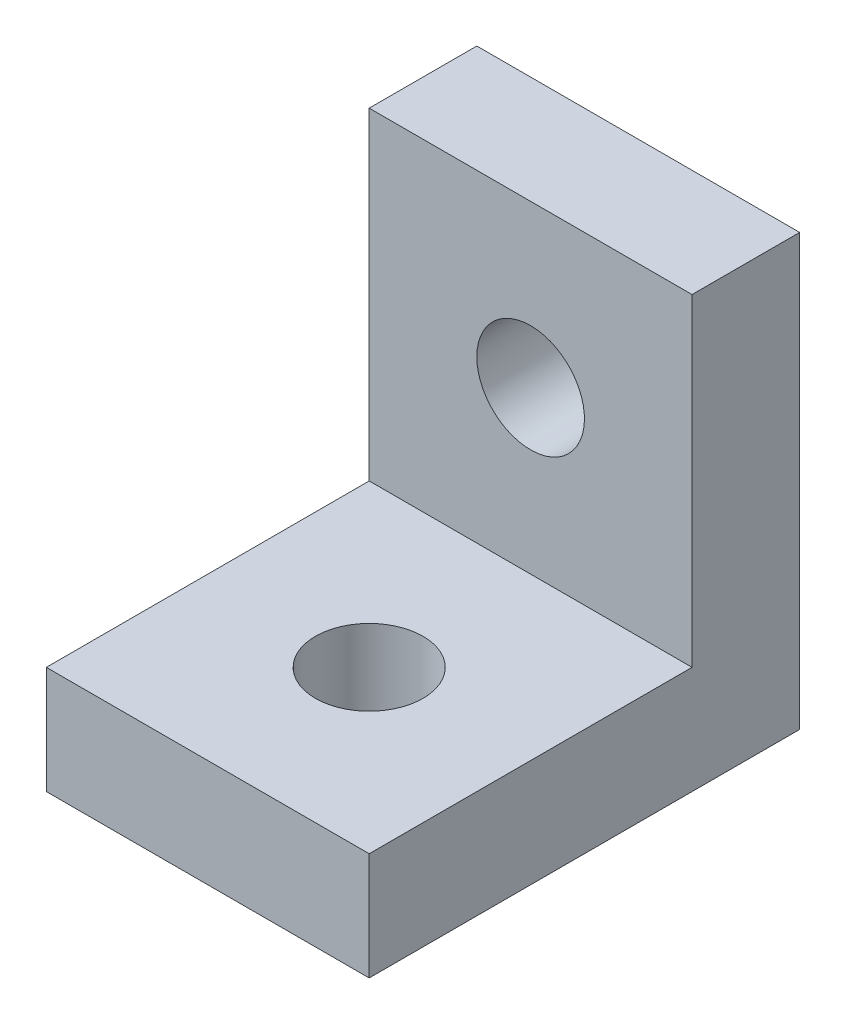
SolidWorks part; units mm, degrees
ref_plane "Front Plane" through (0, 0, 0) normal (0, 0, 1) x (1, 0, 0)
ref_plane "Top Plane" through (0, 0, 0) normal (0, 1, 0) x (1, 0, 0)
ref_plane "Right Plane" through (0, 0, 0) normal (1, 0, 0) x (0, 0, -1)
sketch "Sketch1" plane through (0, 0, 0) normal (1, 0, 0) x (0, 0, -1)
  line L0 (0, 40) -> (0, 0)
  line L1 (0, 0) -> (-40, 0)
  line L2 (-10, 40) -> (-10, 10)
  line L3 (-10, 10) -> (-40, 10)
  line L4 (0, 40) -> (-10, 40)
  line L5 (-40, 0) -> (-40, 10)
  dimension "D1" = 40
  dimension "D2" = 10
extrude "Boss-Extrude1" add sketch "Sketch1" along normal mid plane 30
sketch "Sketch2" plane through (0, 0, 0) normal (0, 0, -1) x (-1, 0, 0)
  line L0 (0, 22) -> (0, -22) construction
  line L1 (-15, 0) -> (15, 0) construction
  circle A0 centre (0, 25) radius 5
  dimension "D2" = 10
  dimension "D1" = 25
extrude "Cut-Extrude1" cut sketch "Sketch2" against normal up to next
sketch "Sketch3" plane through (0, 10, 0) normal (0, 1, 0) x (1, 0, 0)
  line L0 (0, -22) -> (0, 22) construction
  line L1 (15, -40) -> (-15, -40) construction
  circle A0 centre (0, -25) radius 5
  dimension "D1" = 10
  dimension "D2" = 15
extrude "Cut-Extrude2" cut sketch "Sketch3" against normal up to next
